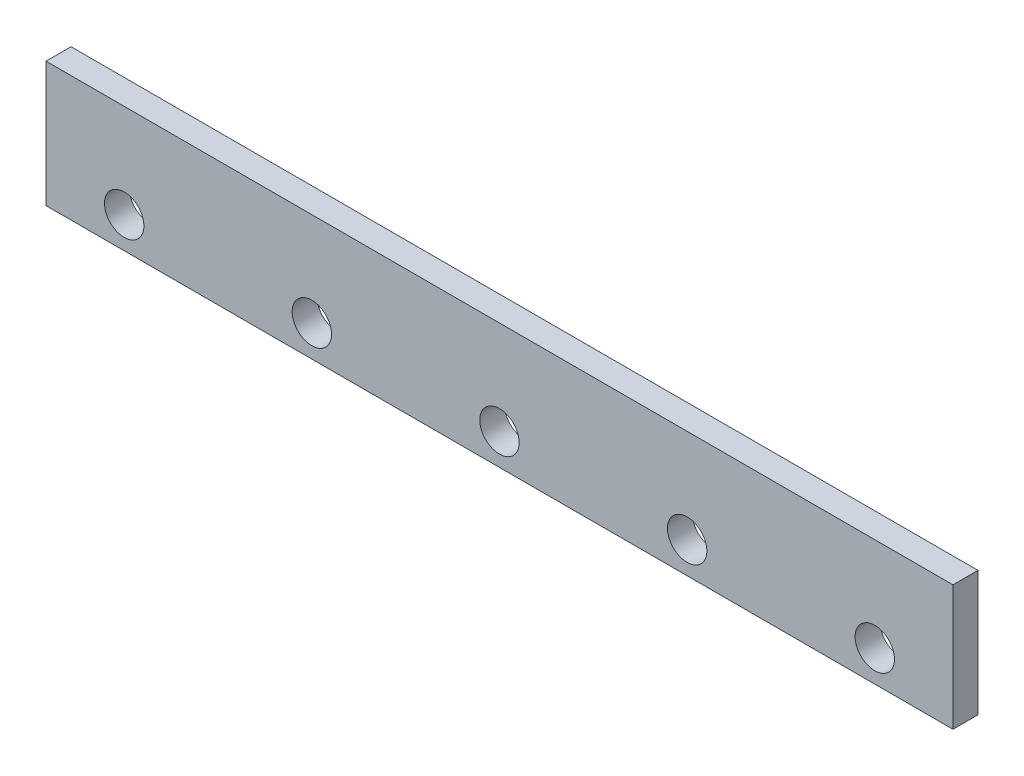
SolidWorks part; units mm, degrees
ref_plane "Front Plane" through (0, 0, 0) normal (0, 0, 1) x (1, 0, 0)
ref_plane "Top Plane" through (0, 0, 0) normal (0, 1, 0) x (1, 0, 0)
ref_plane "Right Plane" through (0, 0, 0) normal (1, 0, 0) x (0, 0, -1)
sketch "Sketch1" plane through (0, 0, 0) normal (0, 0, 1) x (1, 0, 0)
  line L1 (0, 0) -> (580, 0)
  line L2 (0, 0) -> (0, 80)
  line L3 (0, 80) -> (580, 80)
  line L4 (580, 0) -> (580, 80)
  dimension "D1" = 580
  dimension "D2" = 80
extrude "Boss-Extrude1" add sketch "Sketch1" along normal blind 16
sketch "Sketch5" plane through (0, 0, 16) normal (0, 0, 1) x (1, 0, 0)
  circle A0 centre (50, 20) radius 12.6
  circle A1 centre (170, 20) radius 12.6
  circle A2 centre (290, 20) radius 12.6
  circle A3 centre (410, 20) radius 12.6
  circle A4 centre (530, 20) radius 12.6
  dimension "D1" = 25.2
  dimension "D2" = 20
  dimension "D3" = 120
  dimension "D4" = 120
  dimension "D5" = 120
  dimension "D6" = 120
  dimension "D7" = 50
extrude "Cut-Extrude1" cut sketch "Sketch5" against normal blind 16
